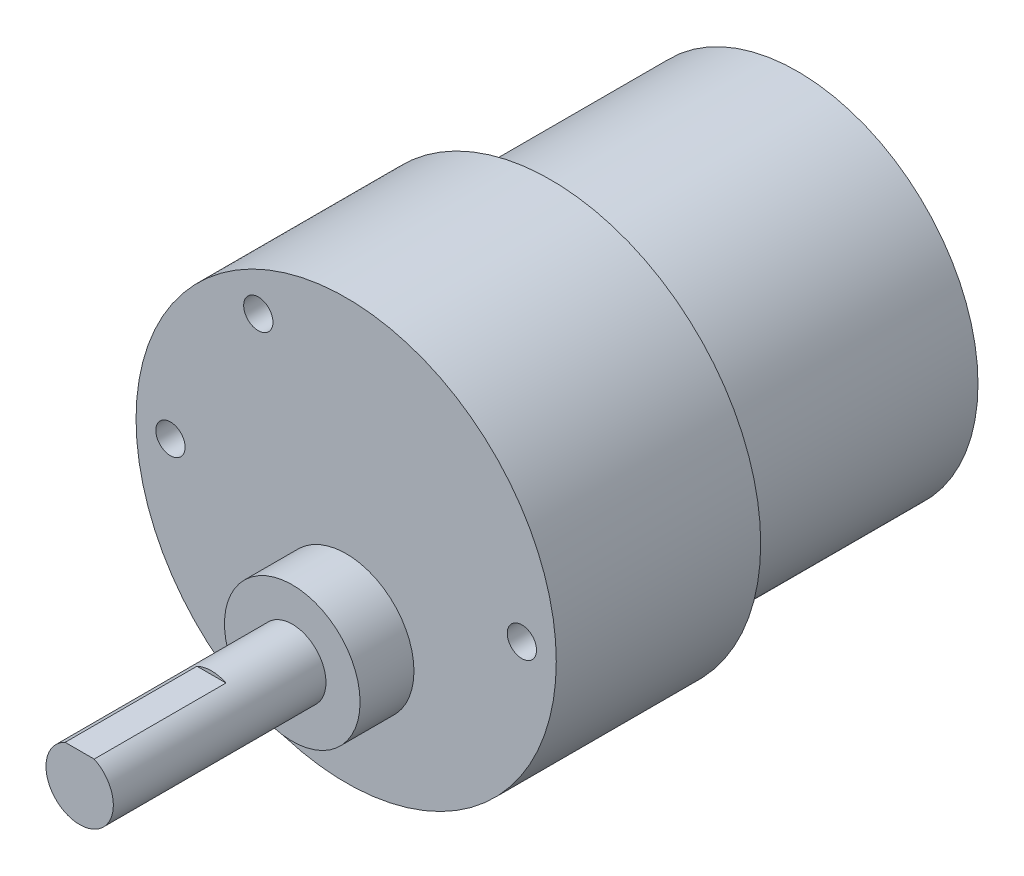
SolidWorks part; units mm, degrees
ref_plane "Front" through (0, 0, 0) normal (0, 0, 1) x (1, 0, 0)
ref_plane "Top" through (0, 0, 0) normal (0, 1, 0) x (1, 0, 0)
ref_plane "Right" through (0, 0, 0) normal (1, 0, 0) x (0, 0, -1)
sketch "Sketch1" plane through (0, 0, 0) normal (0, 0, 1) x (1, 0, 0)
  circle A0 centre (0, 0) radius 15.6591
  dimension "D1" = 31.3182
extrude "motor" add sketch "Sketch1" along normal blind 21.4122
sketch "Sketch3" plane through (0, 0, 21.4122) normal (0, 0, 1) x (1, 0, 0)
  circle A0 centre (0, 0) radius 18.2245
  dimension "D1" = 36.449
extrude "gearbox" add sketch "Sketch3" along normal blind 17.7292
sketch "Sketch4" plane through (0, 0, 39.1414) normal (0, 0, 1) x (1, 0, 0)
  line L0 (-7.4315, -12.7635) -> (7.0599, -12.7635) construction
  line L1 (11.8904, 18.2245) -> (-10.9349, 18.2245) construction
  circle A0 centre (0, -6.8834) radius 5.8801
  circle A1 centre (0, 0) radius 18.2245 construction
  dimension "D2" = 11.7602
  dimension "D1" = 30.988
extrude "protrusion" add sketch "Sketch4" along normal blind 4.6736
sketch "Sketch5" plane through (0, 0, 43.815) normal (0, 0, 1) x (1, 0, 0)
  circle A0 centre (0, -6.8834) radius 2.921
  circle A1 centre (0, -6.8834) radius 5.8801 construction
  dimension "D1" = 5.842
extrude "shaft" add sketch "Sketch5" along normal blind 18.4404
sketch "Sketch6" plane through (0, 0, 39.1414) normal (0, 0, 1) x (1, 0, 0)
  line L0 (13.97, 3.3442) -> (13.97, -4.0342) construction
  line L1 (-13.97, 4.9897) -> (-13.97, -4.512) construction
  line L2 (13.97, 0) -> (0, 0) construction
  line L3 (0, 0) -> (-13.97, 0) construction
  circle A0 centre (15.24, 0) radius 1.27
  circle A1 centre (-15.24, 0) radius 1.27
  circle A2 centre (-7.62, -13.1982) radius 1.27
  circle A3 centre (-7.62, 13.1982) radius 1.27
  dimension "D2" = 2.54
  dimension "D1" = 27.94
  dimension "D3" = 15.24
  dimension "D4" = 6.8834
  dimension "D5" = 6.3148
  dimension "D6" = 7.62
extrude "screw holes" cut sketch "Sketch6" against normal blind 9.3472
sketch "Sketch7" plane through (0, 0, 0) normal (0, 0, -1) x (-1, 0, 0)
  circle A0 centre (0, 0) radius 4.4577
  dimension "D1" = 8.9154
extrude "nub" add sketch "Sketch7" along normal blind 2.921
sketch "Sketch8" plane through (0, 0, 62.2554) normal (0, 0, 1) x (1, 0, 0)
  line L0 (1.26, -4.2481) -> (-1.26, -4.2481)
  line L1 (-2.294, -9.8044) -> (3.1397, -9.8044) construction
  arc A2 (-1.7251, -4.5262) -> (2.0663, -4.8188) centre (0, -6.8834) ccw construction
  arc A3 (1.26, -4.2481) -> (-1.26, -4.2481) centre (0, -6.8834) ccw
  dimension "D2" = 2.921
  dimension "D1" = 5.5562
extrude "Cut-Extrude1" cut sketch "Sketch8" against normal blind 11.43
